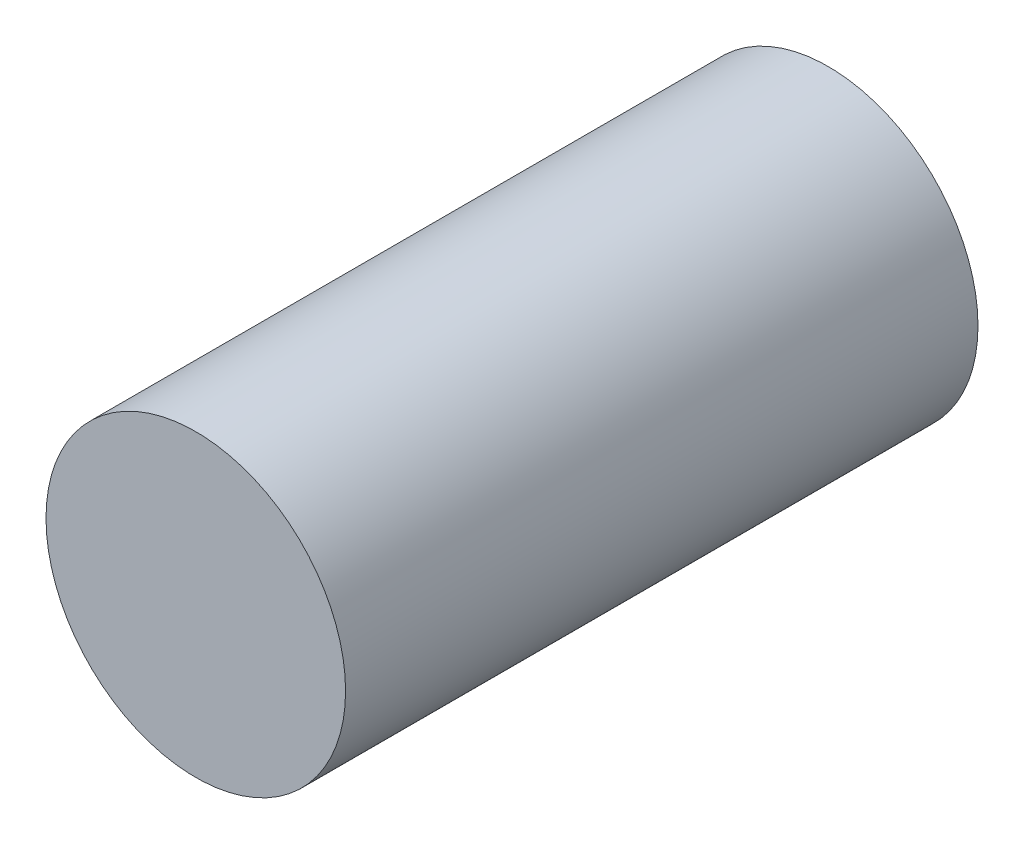
SolidWorks part; units mm, degrees
ref_plane "Front Plane" through (0, 0, 0) normal (0, 0, 1) x (1, 0, 0)
ref_plane "Top Plane" through (0, 0, 0) normal (0, 1, 0) x (1, 0, 0)
ref_plane "Right Plane" through (0, 0, 0) normal (1, 0, 0) x (0, 0, -1)
sketch "Sketch1" plane through (0, 0, 0) normal (0, 0, 1) x (1, 0, 0)
  circle A0 centre (0, 0) radius 18
  dimension "D1" = 36
extrude "Boss-Extrude1" add sketch "Sketch1" against normal blind 76
equation "\"D1@Boss-Extrude1\"=74mm"
